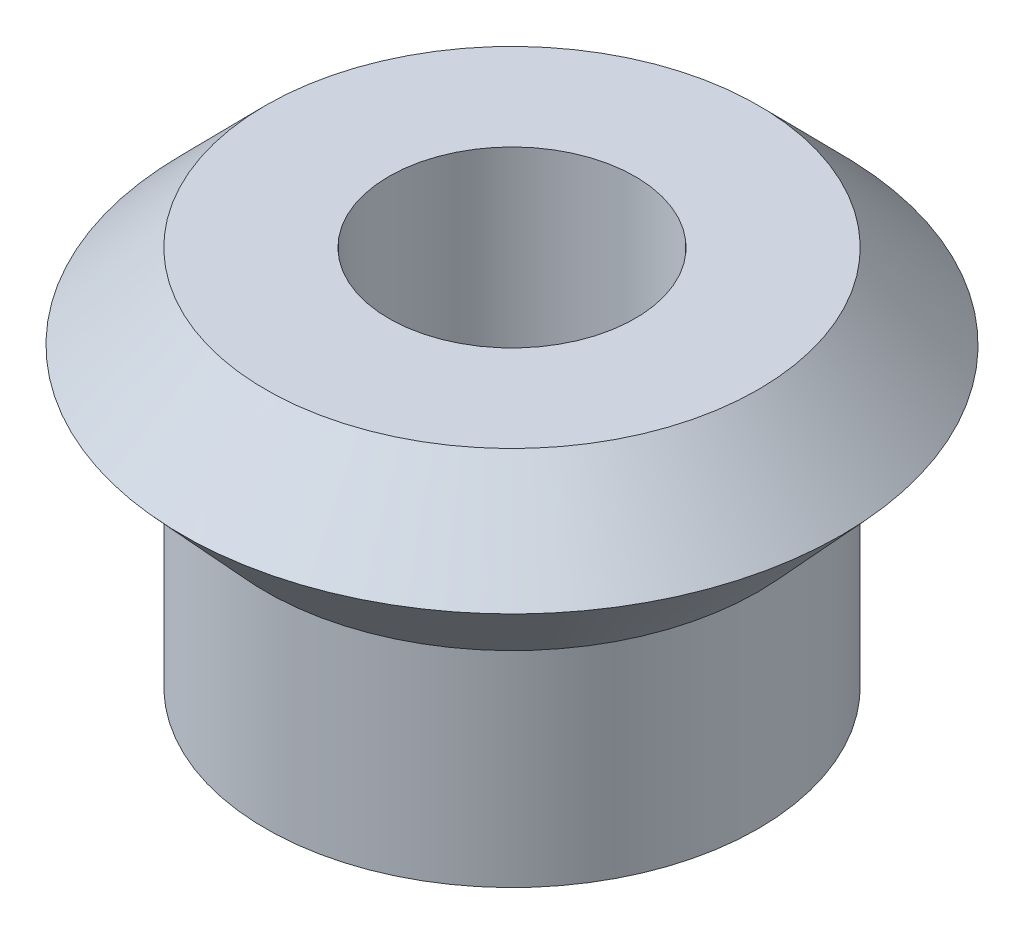
SolidWorks part; units mm, degrees
material "AISI 1045 Steel, cold drawn"
ref_plane "Front Plane" through (0, 0, 0) normal (0, 0, 1) x (1, 0, 0)
ref_plane "Top Plane" through (0, 0, 0) normal (0, 1, 0) x (1, 0, 0)
ref_plane "Right Plane" through (0, 0, 0) normal (1, 0, 0) x (0, 0, -1)
sketch "Sketch3" plane through (0, 0, 0) normal (0, 0, 1) x (1, 0, 0)
  line L1 (0, 0) -> (6, 0)
  line L2 (0, 0) -> (0, 10)
  line L6 (12, 18.53) -> (12, 0) construction
  line L8 (0, 18.53) -> (6, 18.53)
  line L9 (0, 10) -> (-4.06, 14.4177)
  line L10 (-4.06, 14.4177) -> (0, 18.53)
  line L11 (6, 18.53) -> (6, 0)
  line L12 (6, 18.53) -> (12, 18.53) construction
  line L13 (6, 0) -> (12, 0) construction
  dimension "D1" = 12
  dimension "D2" = 18.53
  dimension "D3" = 10
  dimension "D4" = 16.06
  dimension "D5" = 6
  dimension "D6" = 5.7788
  dimension "D7" = 6
revolve "Revolve1" add sketch "Sketch3" angle 360 about L6
